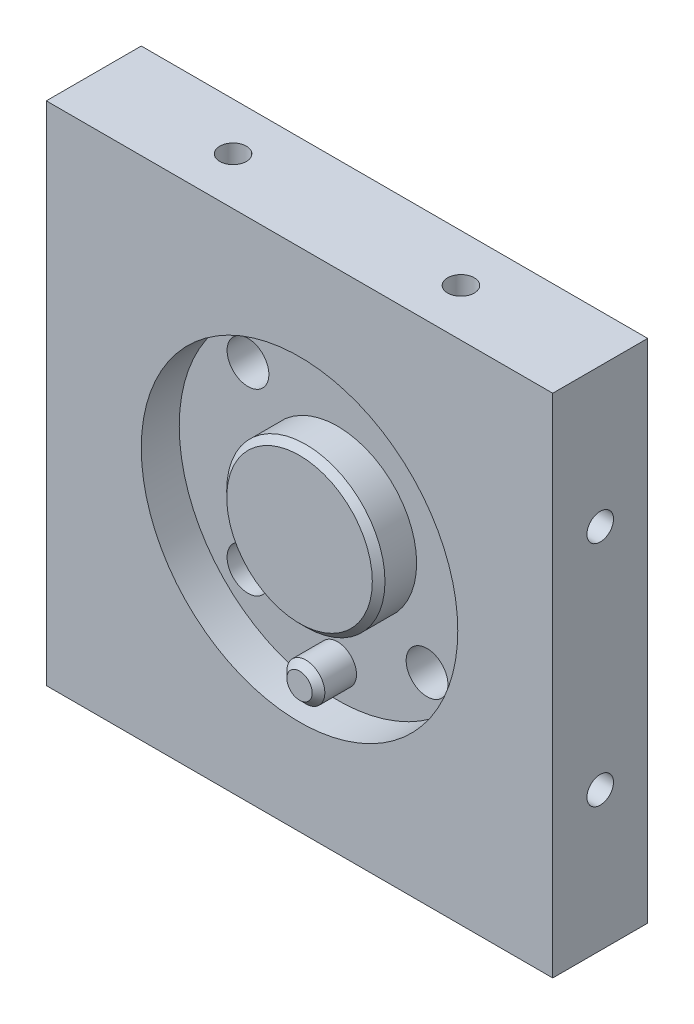
SolidWorks part; units mm, degrees
material "5083-H11"
ref_plane "Front Plane" through (0, 0, 0) normal (0, 0, 1) x (1, 0, 0)
ref_plane "Top Plane" through (0, 0, 0) normal (0, 1, 0) x (1, 0, 0)
ref_plane "Right Plane" through (0, 0, 0) normal (1, 0, 0) x (0, 0, -1)
sketch "Sketch6" plane through (0, 0, 0) normal (0, 0, 1) x (1, 0, 0)
  line L1 (-40, 40) -> (40, 40)
  line L2 (-40, 40) -> (-40, -40)
  line L3 (-40, -40) -> (40, -40)
  line L4 (40, 40) -> (40, -40)
  dimension "D1" = 80
  dimension "D2" = 80
  dimension "D3" = 40
  dimension "D4" = 40
extrude "Extrude2" add sketch "Sketch6" along normal blind 15
sketch "Sketch7" plane through (0, 0, 15) normal (0, 0, 1) x (1, 0, 0)
  circle A0 centre (0, 0) radius 25
  circle A1 centre (0, 0) radius 12.5
  circle A2 centre (0, -20) radius 3
  dimension "D1" = 50
  dimension "D2" = 25
  dimension "D4" = 6
  dimension "D3" = 20
extrude "Extrude3" cut sketch "Sketch7" against normal blind 6
hole_wizard "CBORE for M6 Hex Socket Head Cap Screw1" positions "3DSketch1" profile "Sketch10" counterbore size "M6" standard "ISO"
sketch3d "3DSketch1"
  line L0 (0, 0, 0) -> (13.4485, 13.4485, 0) construction
  line L2 (-40, -40, 0) -> (40, -40, 0) construction
  point P0 (0, 0, 0)
  point P3 (14.1421, 14.1421, 0)
  dimension "D1" = 45
  dimension "D2" = 0
  dimension "D3" = 20
sketch "Sketch10" plane through (14.1421, 14.1421, 0) normal (1, 0, 0) x (0, 1, 0)
  line L0 (0, 0) -> (0, 9.001)
  line L1 (0, 9.001) -> (3.3, 9.001)
  line L3 (3.3, 9.001) -> (3.3, 2)
  line L4 (3.3, 2) -> (5.5, 2)
  line L5 (5.5, 2) -> (5.5, 0)
  line L7 (5.5, 0) -> (0, 0)
  line L11 (0, -6.35) -> (0, 107.95) construction
  dimension "Thru Hole Dia." = 6.6
  dimension "Thru Hole Depth" = 9.001
  dimension "C'Bore Dia." = 11
  dimension "C'Bore Depth" = 2
sketch3d "3DSketch2"
  line L0 (0, 0, 50.455) -> (0, 0, -39.0355)
pattern_circular "CirPattern1" count 4 over 360 about axis through (0, 0, 0) along (0, 0, 1) of "CBORE for M6 Hex Socket Head Cap Screw1"
ref_plane "Plane1" through (0, 0, 0) normal (0, -1, 0) x (1, 0, 0)
chamfer "Chamfer1" distance 1 angle 45 2 edges at (12.5, 0, 15) (3, -20, 15)
hole_wizard "M5 Tapped Hole1" positions "Sketch12" profile "Sketch11" tap size "M5" standard "ISO"
sketch "Sketch12" plane through (40, 0, 0) normal (1, 0, 0) x (0, 0, -1)
  line L0 (-15, -40) -> (0, -40) construction
  point P0 (-7.5, -18)
  point P5 (-7.5, -40)
  dimension "D1" = 22
sketch "Sketch11" plane through (40, -18, 7.5) normal (0, 1, 0) x (0, 0, -1)
  line L0 (0, 0) -> (0, 13.6618)
  line L1 (0, 13.6618) -> (2.1, 12.4)
  line L2 (2.1, 12.4) -> (2.1, 0)
  line L5 (2.1, 0) -> (0, 0)
  line L10 (0, 13.6618) -> (-2.1, 12.4) construction
  line L11 (0, -6.35) -> (0, 107.95) construction
  dimension "Tap Drill Dia." = 4.2
  dimension "Tap Drill Depth" = 12.4
  dimension "Drill Angle" = 118
cosmetic thread "Hole Thread1" parameters "D1"=10, "D2"=5
hole_wizard "M5 Tapped Hole2" positions "Sketch14" profile "Sketch13" tap size "M5" standard "ISO"
sketch "Sketch14" plane through (0, -40, 0) normal (0, -1, 0) x (1, 0, 0)
  line L0 (40, 15) -> (40, 0) construction
  line L1 (-40, 15) -> (-40, 0) construction
  point P0 (18, 7.5)
  point P1 (-18, 7.5)
  point P7 (40, 7.5)
  dimension "D1" = 22
  dimension "D2" = 22
sketch "Sketch13" plane through (18, -40, 7.5) normal (1, 0, 0) x (0, 0, -1)
  line L0 (0, 0) -> (0, 13.6618)
  line L1 (0, 13.6618) -> (2.1, 12.4)
  line L2 (2.1, 12.4) -> (2.1, 0)
  line L5 (2.1, 0) -> (0, 0)
  line L10 (0, 13.6618) -> (-2.1, 12.4) construction
  line L11 (0, -6.35) -> (0, 107.95) construction
  dimension "Tap Drill Dia." = 4.2
  dimension "Tap Drill Depth" = 12.4
  dimension "Drill Angle" = 118
cosmetic thread "Hole Thread2" parameters "D1"=10, "D2"=5
cosmetic thread "Hole Thread3" parameters "D1"=10, "D2"=5
mirror "Mirror1" about plane through (0, 0, 0) normal (1, 0, 0) of "M5 Tapped Hole1"
mirror "Mirror2" about plane through (0, 0, 0) normal (0, -1, 0) of "Mirror1", "M5 Tapped Hole2", "M5 Tapped Hole1"
